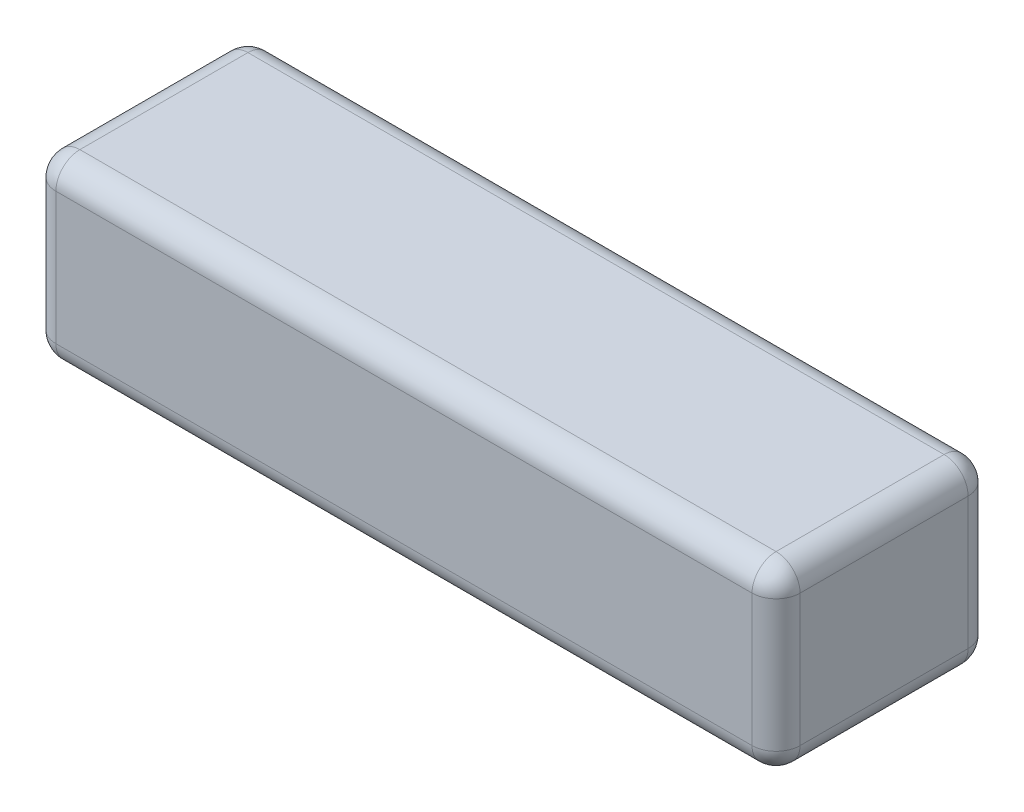
SolidWorks part; units mm, degrees
ref_plane "Front Plane" through (0, 0, 0) normal (0, 0, 1) x (1, 0, 0)
ref_plane "Top Plane" through (0, 0, 0) normal (0, 1, 0) x (1, 0, 0)
ref_plane "Right Plane" through (0, 0, 0) normal (1, 0, 0) x (0, 0, -1)
sketch "Sketch1" plane through (0, 0, 0) normal (0, 1, 0) x (1, 0, 0)
  line L1 (-31, 9) -> (31, 9)
  line L2 (-31, 9) -> (-31, -9)
  line L3 (-31, -9) -> (31, -9)
  line L4 (31, 9) -> (31, -9)
  line L5 (-31, 9) -> (31, -9) construction
  line L6 (-31, -9) -> (31, 9) construction
  point P0 (0, 0)
  dimension "D1" = 62
  dimension "D2" = 18
extrude "Boss-Extrude1" add sketch "Sketch1" along normal mid plane 15
fillet "Fillet1" radius 2 12 edges at (0, -7.5, -9) (-31, -7.5, 0) (0, -7.5, 9) (31, -7.5, 0) (0, 7.5, 9) (-31, 7.5, 0) (0, 7.5, -9) (31, 7.5, 0) (31, 0, -9) (31, 0, 9) (-31, 0, -9) (-31, 0, 9)
